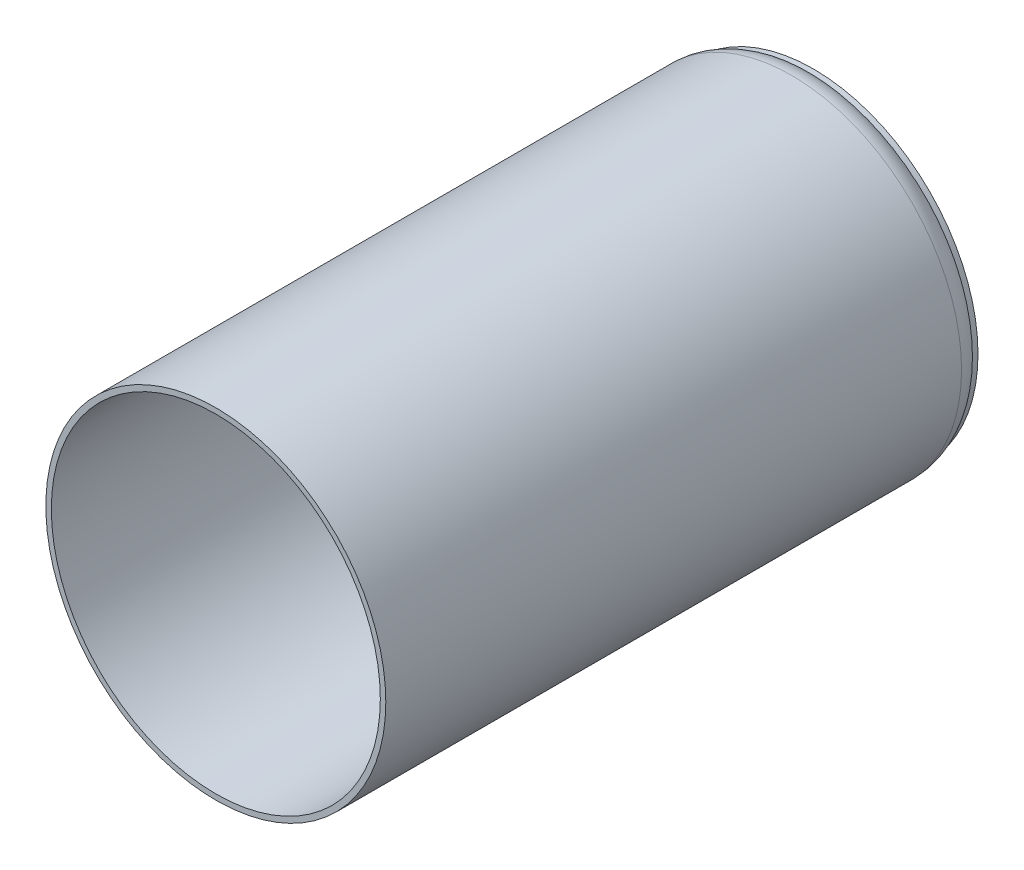
SolidWorks part; units mm, degrees
ref_plane "Front Plane" through (0, 0, 0) normal (0, 0, 1) x (1, 0, 0)
ref_plane "Top Plane" through (0, 0, 0) normal (0, 1, 0) x (1, 0, 0)
ref_plane "Right Plane" through (0, 0, 0) normal (1, 0, 0) x (0, 0, -1)
sketch "Sketch1" plane through (0, 0, 0) normal (0, 0, 1) x (1, 0, 0)
  circle A0 centre (-27.5125, 7.3061) radius 31
  dimension "D1" = 62
extrude "Boss-Extrude1" add sketch "Sketch1" along normal blind 110 contours A0
shell "Shell1" thickness 1
fillet "Fillet2" radius 5 1 edges at (3.4875, 7.3061, 0)
